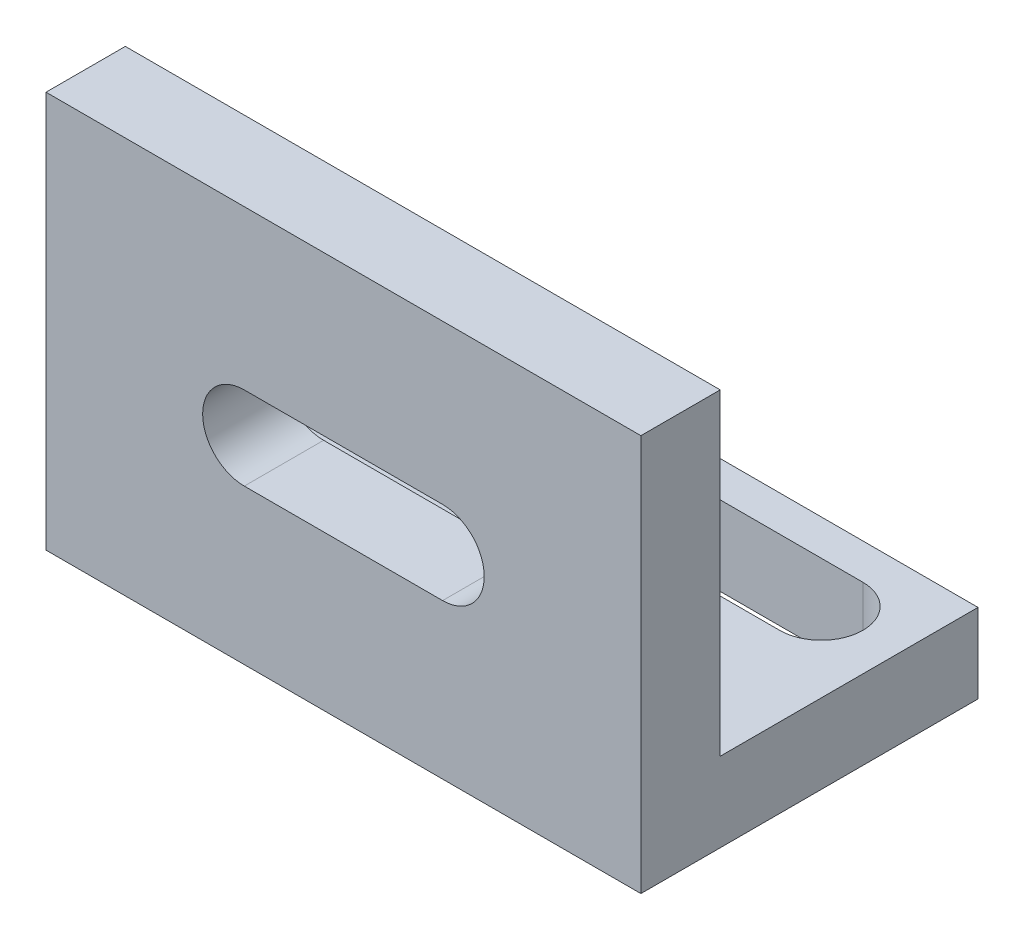
SolidWorks part; units mm, degrees
ref_plane "Front Plane" through (0, 0, 0) normal (0, 0, 1) x (1, 0, 0)
ref_plane "Top Plane" through (0, 0, 0) normal (0, 1, 0) x (1, 0, 0)
ref_plane "Right Plane" through (0, 0, 0) normal (1, 0, 0) x (0, 0, -1)
sketch "Sketch1" plane through (0, 0, 0) normal (0, 1, 0) x (1, 0, 0)
  line L1 (-44.2593, 11.3889) -> (-14.2593, 11.3889)
  line L2 (-44.2593, 11.3889) -> (-44.2593, -5.6111)
  line L4 (-14.2593, 11.3889) -> (-14.2593, -5.6111)
  line L5 (-44.2593, 11.3889) -> (-14.2593, -5.6111) construction
  line L6 (-44.2593, -5.6111) -> (-14.2593, 11.3889) construction
  line L13 (-44.2593, -5.6111) -> (-14.2593, -5.6111)
  line L14 (-44.2593, -5.6111) -> (-44.2593, -4.573)
  line L16 (-14.2593, -5.6111) -> (-14.2593, -4.573)
  point P4 (-29.2593, 2.8889)
  dimension "D1" = 30
  dimension "D2" = 17
extrude "Boss-Extrude1" add sketch "Sketch1" along normal blind 4 contours L2 L13 L4 L1
sketch "Sketch5" plane through (0, 4, 0) normal (0, 1, 0) x (1, 0, 0)
  line L0 (-14.2593, 11.3889) -> (-14.2593, -5.6111) construction
  line L1 (-44.2593, -5.6111) -> (-14.2593, -5.6111)
  line L2 (-44.2593, -5.6111) -> (-44.2593, -1.6111)
  line L3 (-44.2593, -1.6111) -> (-14.2593, -1.6111)
  line L4 (-14.2593, -5.6111) -> (-14.2593, -1.6111)
  line L5 (-44.2593, -5.6111) -> (-14.2593, -1.6111) construction
  line L6 (-44.2593, -1.6111) -> (-14.2593, -5.6111) construction
  point P4 (-29.2593, -3.6111)
  dimension "D1" = 4
extrude "Boss-Extrude2" add sketch "Sketch5" along normal blind 16
sketch "Sketch7" plane through (0, 4, 0) normal (0, 1, 0) x (1, 0, 0)
  line L4 (-18.2593, 7.485) -> (-40.2593, 7.485) construction
  line L5 (-18.2593, 5.385) -> (-40.2593, 5.385)
  line L6 (-18.2593, 9.585) -> (-40.2593, 9.585)
  arc A0 (-18.2593, 5.385) -> (-18.2593, 9.585) centre (-18.2593, 7.485) ccw
  arc A1 (-40.2593, 9.585) -> (-40.2593, 5.385) centre (-40.2593, 7.485) ccw
  point P8 (-29.2593, 7.485)
extrude "Cut-Extrude3" cut sketch "Sketch7" against normal blind 10
sketch "Sketch8" plane through (0, 0, 1.6111) normal (0, 0, -1) x (-1, 0, 0)
  line L8 (24.2593, 9.8972) -> (34.2593, 9.8972) construction
  line L9 (24.2593, 11.9972) -> (34.2593, 11.9972)
  line L10 (24.2593, 7.7972) -> (34.2593, 7.7972)
  arc A2 (24.2593, 11.9972) -> (24.2593, 7.7972) centre (24.2593, 9.8972) ccw
  arc A3 (34.2593, 7.7972) -> (34.2593, 11.9972) centre (34.2593, 9.8972) ccw
  point P6 (29.2593, 9.8972)
extrude "Cut-Extrude5" cut sketch "Sketch8" against normal blind 10
